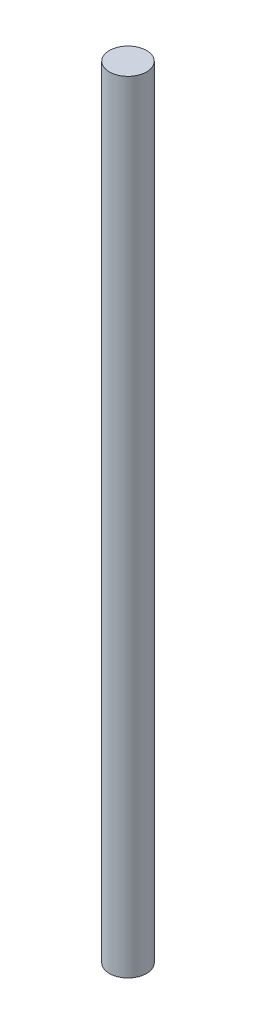
SolidWorks part; units mm, degrees
ref_plane "前视基准面" through (0, 0, 0) normal (0, 0, 1) x (1, 0, 0)
ref_plane "上视基准面" through (0, 0, 0) normal (0, 1, 0) x (1, 0, 0)
ref_plane "右视基准面" through (0, 0, 0) normal (1, 0, 0) x (0, 0, -1)
other "Configuration Table"
sketch "草图1" plane through (0, 0, 0) normal (0, 1, 0) x (1, 0, 0)
  circle A0 centre (0, 0) radius 2
  dimension "D1" = 4
extrude "凸台-拉伸1" add sketch "草图1" along normal blind 84
